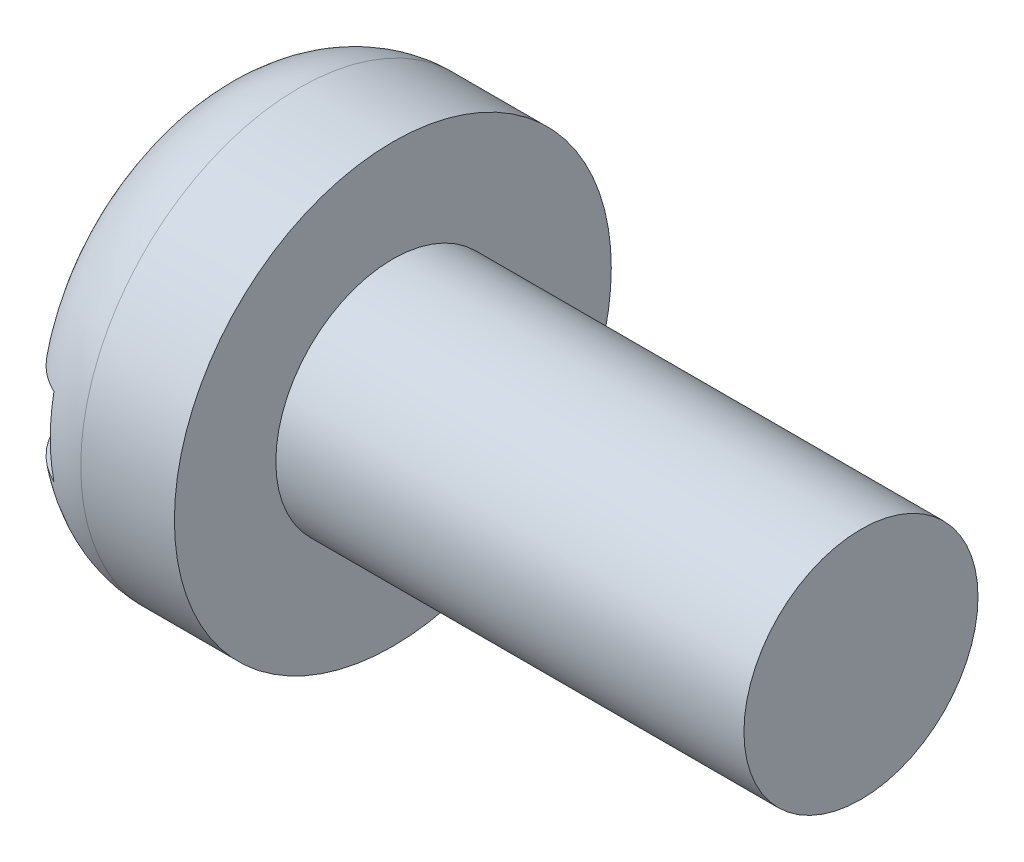
SolidWorks part; units mm, degrees
material "Cast Stainless Steel"
ref_plane "Plane1" through (0, 0, 0) normal (0, 0, 1) x (1, 0, 0)
ref_plane "Plane2" through (0, 0, 0) normal (0, 1, 0) x (1, 0, 0)
ref_plane "Plane3" through (0, 0, 0) normal (1, 0, 0) x (0, 0, -1)
sketch "BodySke" plane through (0, 0, 0) normal (0, 0, 1) x (1, 0, 0)
  line L0 (2.4, 1.5) -> (2.4, 2.8)
  line L1 (0, 0) -> (0, 1.6)
  line L2 (-25.4, 0) -> (127, 0) construction
  line L3 (8.4, 0) -> (0, 0)
  line L4 (2.4, 1.5) -> (8.4, 1.5)
  line L5 (8.4, 1.5) -> (8.4, 0)
  line L6 (1.2, 2.8) -> (2.4, 2.8)
  line L7 (2.4, -1.5) -> (8.4, -1.5) construction
  line L8 (0, -2.8) -> (2.4, -2.8) construction
  line L9 (2.9, 3.0875) -> (2.9, -6.4375) construction
  line L10 (2.4, 6.35) -> (2.4, -3.175) construction
  arc A0 (0, 1.6) -> (1.2, 2.8) centre (1.2, 1.6) cw
  point P15 (0, 2.8)
  dimension "Head_fillet_rad" = 1.2
  dimension "Diameter" = 3
  dimension "Length" = 6
  dimension "Head_ht" = 2.4
  dimension "Head_dia" = 5.6
  dimension "Advance" = 0.5
  dimension "Thread_nom" = 6
revolve "Base-Revolve" add sketch "BodySke" angle 360 about L2
cosmetic thread "ThreadCosmetic" [suppressed] parameters "Thread_length"=5.5, "Thread_minor"=2.439
sketch "Sketch2" plane through (0, 0, 0) normal (1, 0, 0) x (0, 0, -1)
  line L0 (2.8, -0.5) -> (-2.8, -0.5)
  line L1 (2.8, -0.5) -> (2.8, 0.5)
  line L2 (-2.8, 0.5) -> (2.8, 0.5)
  line L3 (-2.8, 0.5) -> (-2.8, -0.5)
  dimension "D1" = 5.6
  dimension "Slot_width" = 1
  dimension "D2" = 2.8
  dimension "D3" = 0.5
extrude "Slot" cut sketch "Sketch2" along normal blind 0.7
sketch "ThdSchSke" plane through (0, 0, 0) normal (0, 0, 1) x (1, 0, 0)
  line L0 (2.9, -1.2195) -> (2.7036, -1.5)
  line L1 (2.9, -1.2195) -> (3.0964, -1.5)
  line L2 (3.0964, -1.5) -> (3.0964, -1.875)
  line L3 (-3.175, 0) -> (5.1513, 0) construction
  line L5 (3.0964, -1.875) -> (2.7036, -1.875)
  line L6 (2.7036, -1.875) -> (2.7036, -1.5)
  dimension "Diameter" = 3
  dimension "SideAngle" = 55
  dimension "VeeAngle" = 70
  dimension "Thread_minor" = 2.439
  dimension "Overcut" = 3.75
  dimension "Start" = 2.9
revolve "ThreadSchematic" [suppressed] cut sketch "ThdSchSke" angle 360 about L3
pattern_linear "ThdSchPat" [suppressed]
equation "\"D1@Sketch2\" = \"Head_dia@BodySke\""
equation "\"D2@Sketch2\" = \"D1@Sketch2\" / 2"
equation "\"D3@Sketch2\" = \"Slot_width@Sketch2\" / 2"
equation "\"Thread_length@ThreadCosmetic\" = ((sgn( (\"Length@BodySke\" - \"Advance@BodySke\" ) - \"Thread_nom@BodySke\" )-1)*( (\"Length@BodySke\" - \"Advance@BodySke\" ) - \"Thread_nom@BodySke\" ))/-2+ \"Thread_nom@BodySke\""
equation "\"Thread_minor@ThdSchSke\" = \"Thread_minor@ThreadCosmetic\""
equation "\"Diameter@ThdSchSke\" = \"Diameter@BodySke\""
equation "\"Overcut@ThdSchSke\" = \"Diameter@BodySke\" * 1.25"
equation "\"Start@ThdSchSke\" = \"Head_ht@BodySke\" + \"Length@BodySke\" - \"Thread_length@ThreadCosmetic\"  '---Non-countersunk---"
equation "\"Num_threads@ThdSchPat\" = int( \"Thread_length@ThreadCosmetic\" / \"Advance@BodySke\" + 0.999 )  + 1"
equation "\"Advance@ThdSchPat\" = \"Thread_length@ThreadCosmetic\" /  (\"Num_threads@ThdSchPat\" - 1) 'relax it"
